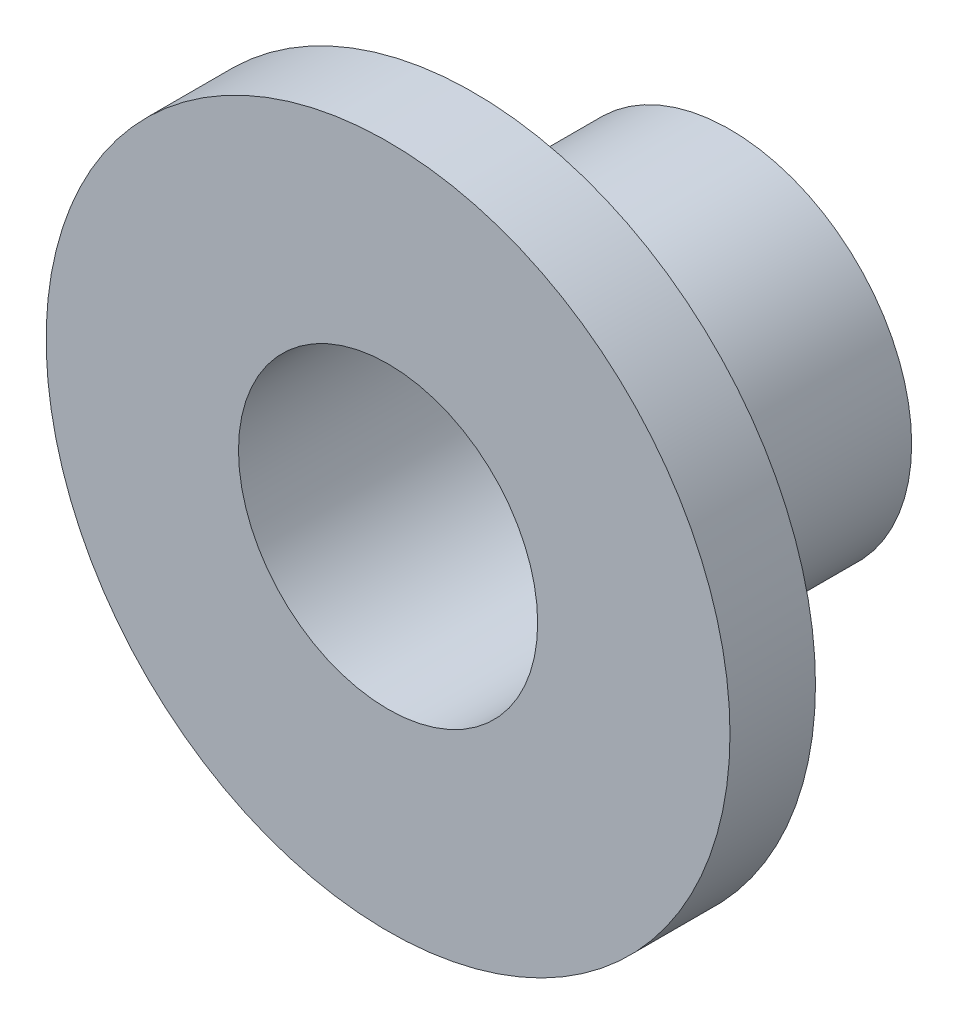
SolidWorks part; units mm, degrees
ref_plane "Front Plane" through (0, 0, 0) normal (0, 0, 1) x (1, 0, 0)
ref_plane "Top Plane" through (0, 0, 0) normal (0, 1, 0) x (1, 0, 0)
ref_plane "Right Plane" through (0, 0, 0) normal (1, 0, 0) x (0, 0, -1)
sketch "Sketch1" plane through (0, 0, 0) normal (0, 0, 1) x (1, 0, 0)
  circle A0 centre (0, 0) radius 1.75
  circle A1 centre (0, 0) radius 2.125
  dimension "D1" = 3.5
  dimension "D2" = 4.25
extrude "Boss-Extrude1" add sketch "Sketch1" along normal blind 3
sketch "Sketch2" plane through (0, 0, 3) normal (0, 0, 1) x (1, 0, 0)
  circle A0 centre (0, 0) radius 4
  circle A1 centre (0, 0) radius 1.75
  dimension "D1" = 3.5
  dimension "D2" = 8
extrude "Boss-Extrude2" add sketch "Sketch2" along normal blind 1
